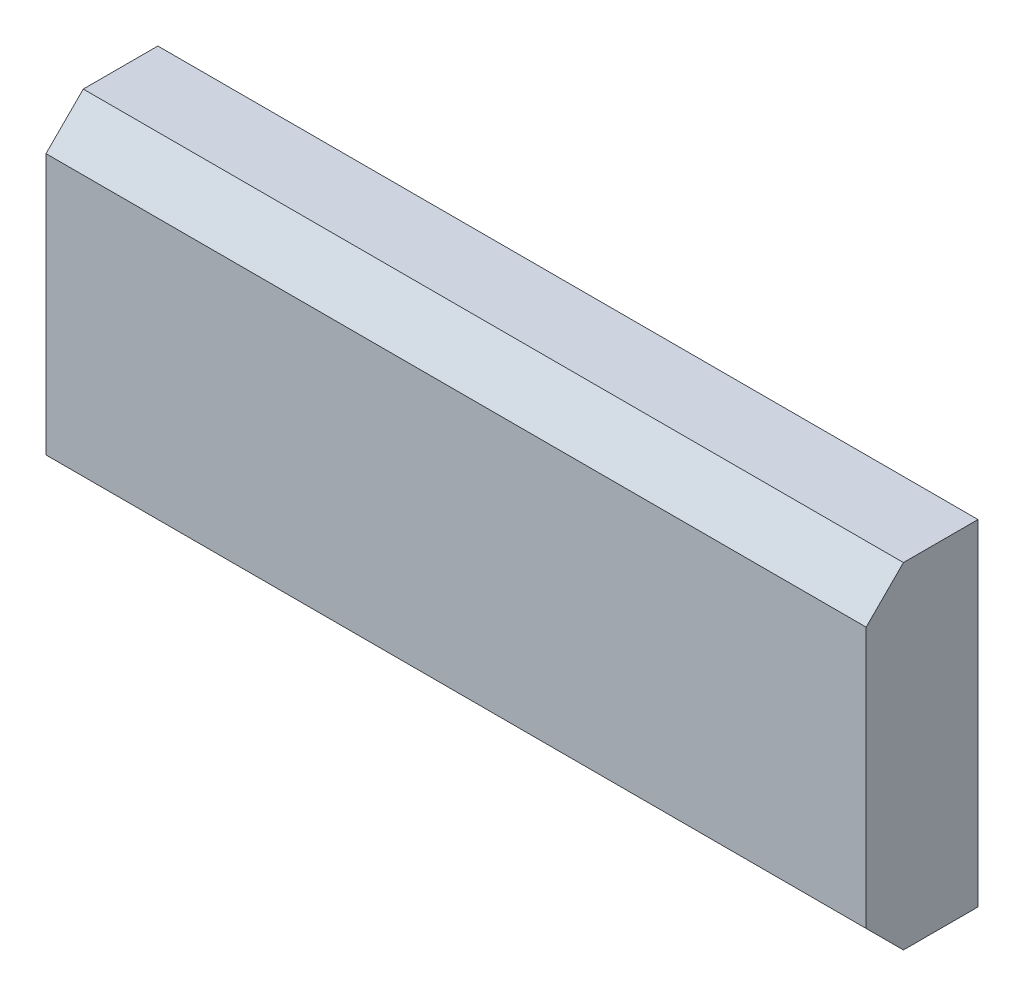
SolidWorks part; units mm, degrees
material "Стекло"
ref_plane "Front" through (0, 0, 0) normal (0, 0, 1) x (1, 0, 0)
ref_plane "Top" through (0, 0, 0) normal (0, 1, 0) x (1, 0, 0)
ref_plane "Right" through (0, 0, 0) normal (1, 0, 0) x (0, 0, -1)
sketch "Эскиз1" plane through (0, 0, 0) normal (0, 0, 1) x (1, 0, 0)
  line L1 (-11, -4.5) -> (11, -4.5)
  line L2 (-11, -4.5) -> (-11, 4.5)
  line L3 (-11, 4.5) -> (11, 4.5)
  line L4 (11, -4.5) -> (11, 4.5)
  dimension "D1" = 22
  dimension "D2" = 9
  dimension "D3" = 4.5
  dimension "D4" = 11
extrude "Вытянуть1" add sketch "Эскиз1" along normal blind 3
chamfer "Фаска1" distance 1 angle 45 2 edges at (0, 4.5, 3) (0, -4.5, 3)
